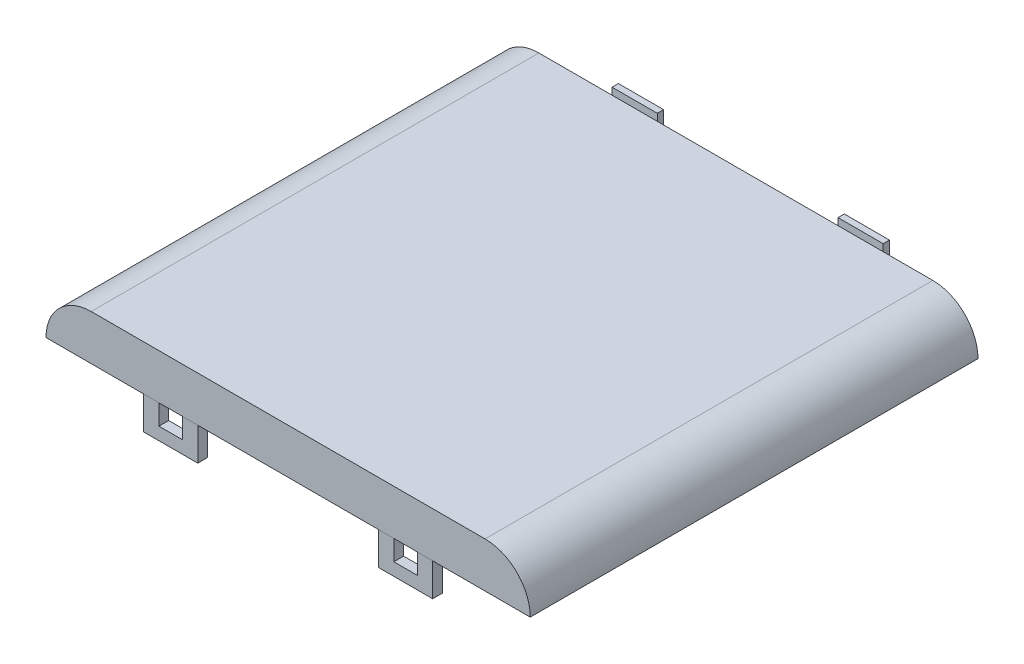
SolidWorks part; units mm, degrees
ref_plane "Front Plane" through (0, 0, 0) normal (0, 0, 1) x (1, 0, 0)
ref_plane "Top Plane" through (0, 0, 0) normal (0, 1, 0) x (1, 0, 0)
ref_plane "Right Plane" through (0, 0, 0) normal (1, 0, 0) x (0, 0, -1)
sketch "Sketch1" plane through (0, 0, 0) normal (0, 1, 0) x (1, 0, 0)
  line L1 (34.036, -31.4706) -> (-34.036, -31.4706)
  line L2 (34.036, -31.4706) -> (34.036, 31.4706)
  line L3 (34.036, 31.4706) -> (-34.036, 31.4706)
  line L4 (-34.036, -31.4706) -> (-34.036, 31.4706)
  line L5 (34.036, -31.4706) -> (-34.036, 31.4706) construction
  line L6 (34.036, 31.4706) -> (-34.036, -31.4706) construction
  point P0 (0, 0)
  dimension "D1" = 68.072
  dimension "D2" = 62.9412
extrude "Boss-Extrude1" add sketch "Sketch1" along normal blind 18.9103
fillet "Fillet1" radius 6.35 4 edges at (-34.036, 0, 0) (34.036, 0, 0) (34.036, 18.9103, 0) (-34.036, 18.9103, 0)
sketch "Sketch36" plane through (34.036, 0, 0) normal (1, 0, 0) x (0, 0, -1)
  line L0 (31.4706, 0) -> (-31.4706, 0) construction
  line L1 (-31.4706, 12.5603) -> (31.4706, 12.5603)
  line L2 (-31.4706, 12.5603) -> (-31.4706, 0)
  line L3 (-31.4706, 0) -> (31.4706, 0)
  line L4 (31.4706, 12.5603) -> (31.4706, 0)
  line L5 (31.4706, 12.5603) -> (31.4706, 18.9103) construction
extrude "Cut-Extrude13" cut sketch "Sketch36" against normal through all both and the other way through all
sketch "Sketch37" plane through (0, 0, 31.4706) normal (0, 0, 1) x (1, 0, 0)
  line L0 (-34.036, 12.5603) -> (34.036, 12.5603) construction
  line L1 (-20.32, 12.5603) -> (-12.7, 12.5603)
  line L2 (-20.32, 12.5603) -> (-20.32, 7.9375)
  line L3 (-20.32, 7.9375) -> (-12.7, 7.9375)
  line L4 (-12.7, 12.5603) -> (-12.7, 7.9375)
  line L5 (0, 0) -> (0, 12.5603) construction
  line L6 (14.859, 12.5603) -> (14.859, 9.7155)
  line L7 (-18.161, 12.5603) -> (-14.859, 12.5603)
  line L8 (-18.161, 12.5603) -> (-18.161, 9.7155)
  line L9 (-18.161, 9.7155) -> (-14.859, 9.7155)
  line L10 (-14.859, 12.5603) -> (-14.859, 9.7155)
  line L11 (18.161, 9.7155) -> (14.859, 9.7155)
  line L12 (18.161, 12.5603) -> (18.161, 9.7155)
  line L13 (18.161, 12.5603) -> (14.859, 12.5603)
  line L14 (12.7, 12.5603) -> (12.7, 7.9375)
  line L15 (20.32, 7.9375) -> (12.7, 7.9375)
  line L16 (20.32, 12.5603) -> (20.32, 7.9375)
  line L17 (20.32, 12.5603) -> (12.7, 12.5603)
  line M10 (-34.036, 12.5603) -> (34.036, 12.5603)
  dimension "D1" = 12.7
  dimension "D2" = 7.62
  dimension "D3" = 4.6228
  dimension "D4" = 1.778
  dimension "D5" = 2.159
  dimension "D6" = 2.159
extrude "Boss-Extrude2" add sketch "Sketch37" against normal blind 1.3716 separate body contours L10 L9 L8 L2 L3 L4 M10 | L16 L12 L11 L6 L14 L15 M10
shell "Shell1" thickness 1.3716
sketch "Sketch40" plane through (0, 0, -31.4706) normal (0, 0, -1) x (-1, 0, 0)
  line L0 (27.686, 15.8623) -> (-27.686, 15.8623)
  line L2 (-34.036, 12.5603) -> (34.036, 12.5603)
  line L3 (27.686, 18.9103) -> (-27.686, 18.9103)
  line L4 (-30.988, 12.5603) -> (30.988, 12.5603)
  line L6 (-28.956, 15.6083) -> (28.956, 15.6083) construction
  line L8 (-34.036, 12.5603) -> (34.036, 12.5603) construction
  line L9 (27.686, 18.9103) -> (-27.686, 18.9103) construction
  arc A2 (-27.686, 18.9103) -> (-34.036, 12.5603) centre (-27.686, 12.5603) ccw
  arc A3 (34.036, 12.5603) -> (27.686, 18.9103) centre (27.686, 12.5603) ccw
  arc A6 (30.988, 12.5603) -> (27.686, 15.8623) centre (27.686, 12.5603) ccw
  arc A7 (28.956, 15.6083) -> (27.686, 15.8623) centre (27.686, 12.5603) ccw construction
  arc A8 (-27.686, 15.8623) -> (-28.956, 15.6083) centre (-27.686, 12.5603) ccw construction
  arc A9 (-27.686, 15.8623) -> (-30.988, 12.5603) centre (-27.686, 12.5603) ccw
  arc A10 (-27.686, 18.9103) -> (-34.036, 12.5603) centre (-27.686, 12.5603) ccw construction
  arc A11 (34.036, 12.5603) -> (27.686, 18.9103) centre (27.686, 12.5603) ccw construction
  dimension "D1" = 0
  dimension "D2" = 3.048
extrude "Cut-Extrude14" cut sketch "Sketch40" against normal blind 1.3716
sketch "Sketch41" plane through (0, 0, -31.4706) normal (0, 0, -1) x (-1, 0, 0)
  line L0 (27.686, 15.8623) -> (-27.686, 15.8623) construction
  line L1 (-19.05, 15.8623) -> (-12.7, 15.8623)
  line L2 (-19.05, 15.8623) -> (-19.05, 19.5072)
  line L3 (-19.05, 19.5072) -> (-12.7, 19.5072)
  line L4 (-12.7, 15.8623) -> (-12.7, 19.5072)
  line L5 (-19.05, 19.5072) -> (-19.05, 17.2212) construction
  line L6 (12.7, 19.5072) -> (12.7, 17.2212) construction
  line L7 (12.7, 15.8623) -> (19.05, 15.8623)
  line L8 (12.7, 15.8623) -> (12.7, 19.5072)
  line L9 (12.7, 19.5072) -> (19.05, 19.5072)
  line L10 (19.05, 15.8623) -> (19.05, 19.5072)
extrude "Boss-Extrude4" add sketch "Sketch41" along normal blind 2.54
sketch "Sketch42" plane through (0, 0, -34.0106) normal (0, 0, -1) x (-1, 0, 0)
  line L0 (19.05, 15.8623) -> (19.05, 19.5072) construction
  line L1 (-19.05, 19.5072) -> (19.05, 19.5072)
  line L2 (-19.05, 19.5072) -> (-19.05, 18.2372)
  line L3 (-19.05, 18.2372) -> (19.05, 18.2372)
  line L4 (19.05, 19.5072) -> (19.05, 18.2372)
  dimension "D1" = 1.27
extrude "Cut-Extrude15" cut sketch "Sketch42" against normal up to surface (2.54 mm away) up to face at (-26.7492, 16.1108, -31.4706)
sketch "Sketch43" plane through (-19.05, 0, 0) normal (-1, 0, 0) x (0, 0, 1)
  line L0 (-31.4706, 18.2372) -> (-34.0106, 18.2372) construction
  line L1 (-33.1248, 18.2372) -> (-31.4706, 18.2372)
  line L2 (-33.1248, 18.2372) -> (-33.1248, 16.8258)
  line L3 (-33.1248, 16.8258) -> (-31.4706, 16.8258)
  line L4 (-31.4706, 18.2372) -> (-31.4706, 16.8258)
  line L5 (-31.4706, 15.8623) -> (-31.4706, 18.2372) construction
extrude "Cut-Extrude16" cut sketch "Sketch43" against normal through all
